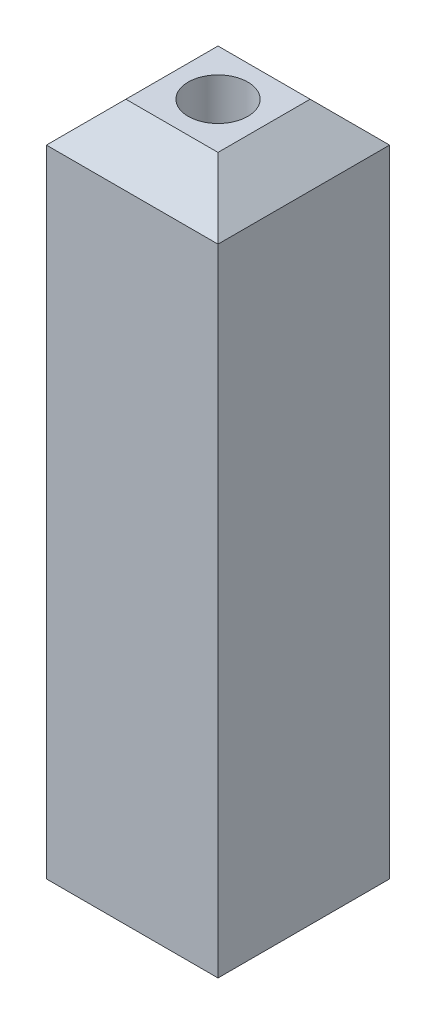
SolidWorks part; units mm, degrees
ref_plane "Front Plane" through (0, 0, 0) normal (0, 0, 1) x (1, 0, 0)
ref_plane "Top Plane" through (0, 0, 0) normal (0, 1, 0) x (1, 0, 0)
ref_plane "Right Plane" through (0, 0, 0) normal (1, 0, 0) x (0, 0, -1)
sketch "Sketch1" plane through (0, 0, 0) normal (0, 1, 0) x (1, 0, 0)
  line L1 (-27.432, 27.432) -> (27.432, 27.432)
  line L2 (-27.432, 27.432) -> (-27.432, -27.432)
  line L3 (-27.432, -27.432) -> (27.432, -27.432)
  line L4 (27.432, 27.432) -> (27.432, -27.432)
  line L5 (-27.432, 27.432) -> (27.432, -27.432) construction
  line L6 (-27.432, -27.432) -> (27.432, 27.432) construction
  point P0 (0, 0)
  dimension "D1" = 54.864
  dimension "D2" = 54.864
extrude "Boss-Extrude2" add sketch "Sketch1" along normal blind 215.9 contours L2 L3 L4 L1
hole_wizard "3/4 (0.75) Diameter Hole1" positions "Sketch4" profile "Sketch6" hole size "3/4" standard "ANSI Inch"
sketch "Sketch4" plane through (0, 0, 0) normal (0, -1, 0) x (1, 0, 0)
  point P0 (0, 0)
  point P4 (0, 0)
  point P5 (0, 0)
sketch "Sketch6" plane through (0, 0, 0) normal (1, 0, 0) x (0, 0, -1)
  line L0 (0, 0) -> (0, 158.1232)
  line L1 (0, 158.1232) -> (9.525, 152.4)
  line L2 (9.525, 152.4) -> (9.525, 0)
  line L5 (9.525, 0) -> (0, 0)
  line L10 (0, 158.1232) -> (-9.525, 152.4) construction
  line L11 (0, -6.35) -> (0, 107.95) construction
  dimension "Hole Dia." = 19.05
  dimension "Hole Depth" = 152.4
  dimension "Drill Angle" = 118
hole_wizard "13/64 (0.20313) Diameter Hole1" positions "Sketch7" profile "Sketch8" hole size "13/64" standard "ANSI Inch"
sketch "Sketch7" plane through (0, 0, 0) normal (0, -1, 0) x (1, 0, 0)
  line L0 (-27.432, -27.432) -> (-27.432, 27.432) construction
  line L1 (-27.432, 27.432) -> (27.432, 27.432) construction
  point P0 (-23.622, 23.622)
  point P2 (23.622, 23.622)
  point P4 (23.622, -23.622)
  point P6 (-23.622, -23.622)
  point P9 (0, 0)
  point P14 (0, 0)
  point P15 (0, 0)
  point P16 (0, 0)
  point P17 (0, 0)
  point P18 (0, 0)
  point P19 (0, 0)
  point P24 (0, 0)
  dimension "D1" = 3.81
  dimension "D2" = 3.81
  dimension "D3" = 47.244
  dimension "D4" = 47.244
sketch "Sketch8" plane through (-23.622, 0, 23.622) normal (1, 0, 0) x (0, 0, -1)
  line L0 (0, 0) -> (0, 153.9501)
  line L1 (0, 153.9501) -> (2.5798, 152.4)
  line L2 (2.5798, 152.4) -> (2.5798, 0)
  line L5 (2.5798, 0) -> (0, 0)
  line L10 (0, 153.9501) -> (-2.5798, 152.4) construction
  line L11 (0, -6.35) -> (0, 107.95) construction
  dimension "Hole Dia." = 5.1595
  dimension "Hole Depth" = 152.4
  dimension "Drill Angle" = 118
hole_wizard "3/4 (0.75) Diameter Hole2" positions "Sketch9" profile "Sketch10" hole size "3/4" standard "ANSI Inch"
sketch "Sketch9" plane through (0, 215.9, 0) normal (0, 1, 0) x (-1, 0, 0)
  point P0 (0, 0)
sketch "Sketch10" plane through (0, 215.9, 0) normal (1, 0, 0) x (0, 0, 1)
  line L0 (0, 0) -> (0, 48.2682)
  line L1 (0, 48.2682) -> (9.525, 42.545)
  line L2 (9.525, 42.545) -> (9.525, 0)
  line L5 (9.525, 0) -> (0, 0)
  line L10 (0, 48.2682) -> (-9.525, 42.545) construction
  line L11 (0, -6.35) -> (0, 107.95) construction
  dimension "Hole Dia." = 19.05
  dimension "Hole Depth" = 42.545
  dimension "Drill Angle" = 118
chamfer "Chamfer1" distance 12.7 angle 45 4 edges at (0, 215.9, 27.432) (-27.432, 215.9, 0) (27.432, 215.9, 0) (0, 215.9, -27.432)
